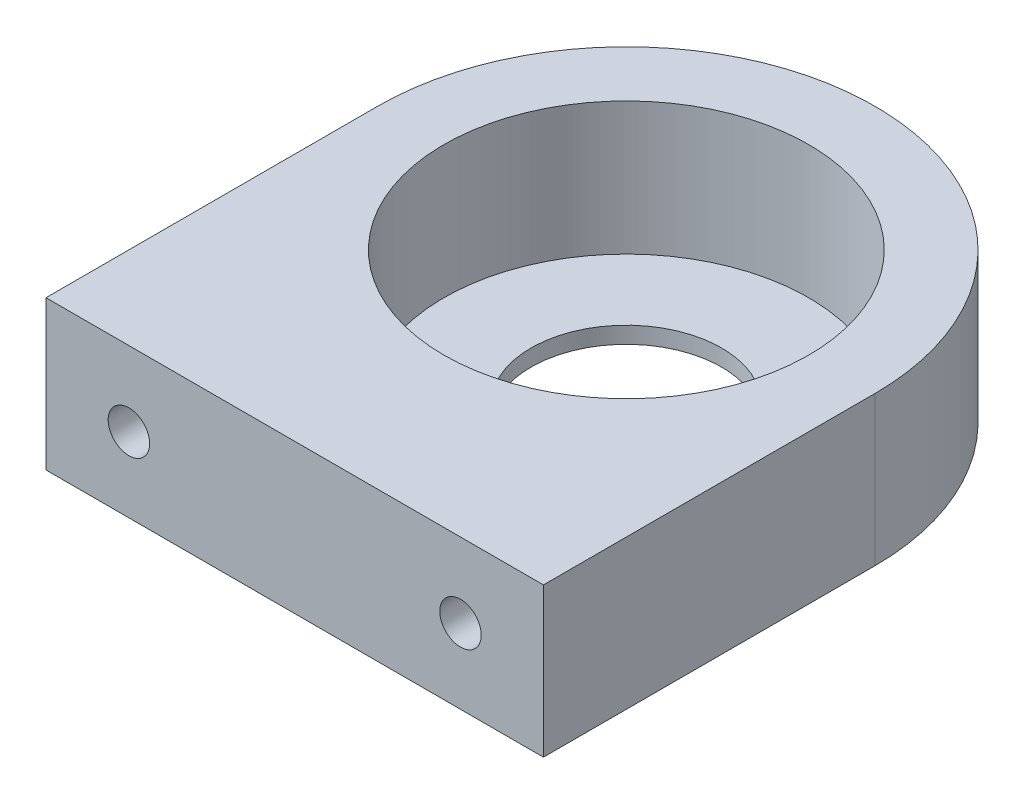
SolidWorks part; units mm, degrees
ref_plane "Front Plane" through (0, 0, 0) normal (0, 0, 1) x (1, 0, 0)
ref_plane "Top Plane" through (0, 0, 0) normal (0, 1, 0) x (1, 0, 0)
ref_plane "Right Plane" through (0, 0, 0) normal (1, 0, 0) x (0, 0, -1)
sketch "Sketch1" plane through (0, 0, 0) normal (0, 1, 0) x (1, 0, 0)
  line L0 (30, 0) -> (0, 0)
  line L1 (0, 0) -> (0, 20)
  line L2 (30, 0) -> (30, 20)
  arc A0 (30, 20) -> (0, 20) centre (15, 20) ccw
  circle A1 centre (15, 20) radius 11
  circle A2 centre (15, 20) radius 5.75
  dimension "D1" = 30
  dimension "D3" = 22
  dimension "D4" = 11.5
  dimension "D2" = 20
extrude "Boss-Extrude1" add sketch "Sketch1" along normal blind 9 contours L2 A0 L1 L0 A1 | A1 A2
sketch "Sketch2" plane through (0, 9, 0) normal (0, 1, 0) x (1, 0, 0)
  circle A0 centre (15, 20) radius 11
  circle A1 centre (15, 20) radius 5.75 construction
  dimension "D1" = 22
extrude "Cut-Extrude1" cut sketch "Sketch2" against normal blind 8
sketch "Sketch8" plane through (0, 0, 0) normal (0, 0, 1) x (1, 0, 0)
  line L0 (15, 9) -> (15, 0) construction
  line L1 (30, 9) -> (0, 9) construction
  line L2 (30, 0) -> (0, 0) construction
  line L3 (15, 0) -> (15, 4.5) construction
  line L5 (0, 9) -> (0, 0) construction
  line L7 (30, 9) -> (30, 0) construction
  line L8 (5, 4.5) -> (0, 4.5) construction
  line L9 (5, 4.5) -> (0, 4.5) construction
  line L10 (25, 4.5) -> (30, 4.5) construction
  circle A0 centre (25, 4.5) radius 1.25
  circle A1 centre (5, 4.5) radius 1.25
  dimension "D1" = 2.5
  dimension "D2" = 2.5
  dimension "D3" = 20
extrude "Cut-Extrude2" cut sketch "Sketch8" against normal blind 10
sketch "Sketch11" plane through (0, 0, 0) normal (0, 0, 1) x (1, 0, 0)
  circle A0 centre (5, 4.5) radius 2.4265
  circle A1 centre (25, 4.5) radius 2.5317
